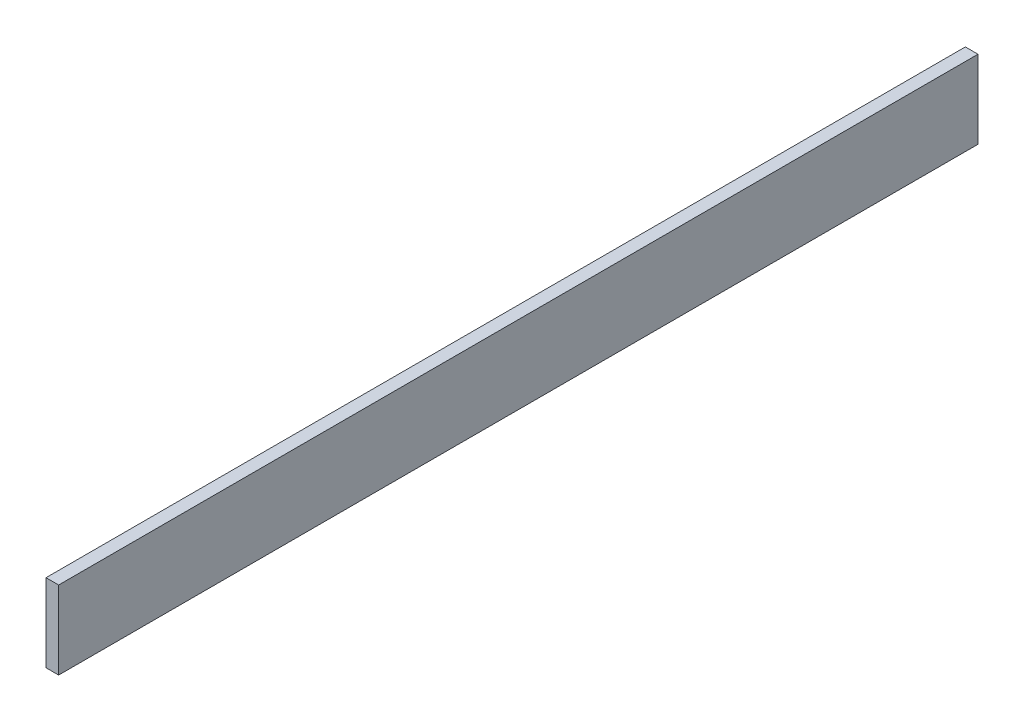
SolidWorks part; units mm, degrees
ref_plane "Front Plane" through (0, 0, 0) normal (0, 0, 1) x (1, 0, 0)
ref_plane "Top Plane" through (0, 0, 0) normal (0, 1, 0) x (1, 0, 0)
ref_plane "Right Plane" through (0, 0, 0) normal (1, 0, 0) x (0, 0, -1)
sketch "Sketch1" plane through (0, 0, 0) normal (1, 0, 0) x (0, 0, -1)
  line L1 (0, 0) -> (2768.6, 0)
  line L2 (0, 0) -> (0, 234.95)
  line L3 (0, 234.95) -> (2768.6, 234.95)
  line L4 (2768.6, 0) -> (2768.6, 234.95)
  dimension "D1" = 2768.6
  dimension "D2" = 234.95
extrude "Boss-Extrude1" add sketch "Sketch1" along normal blind 38.1
